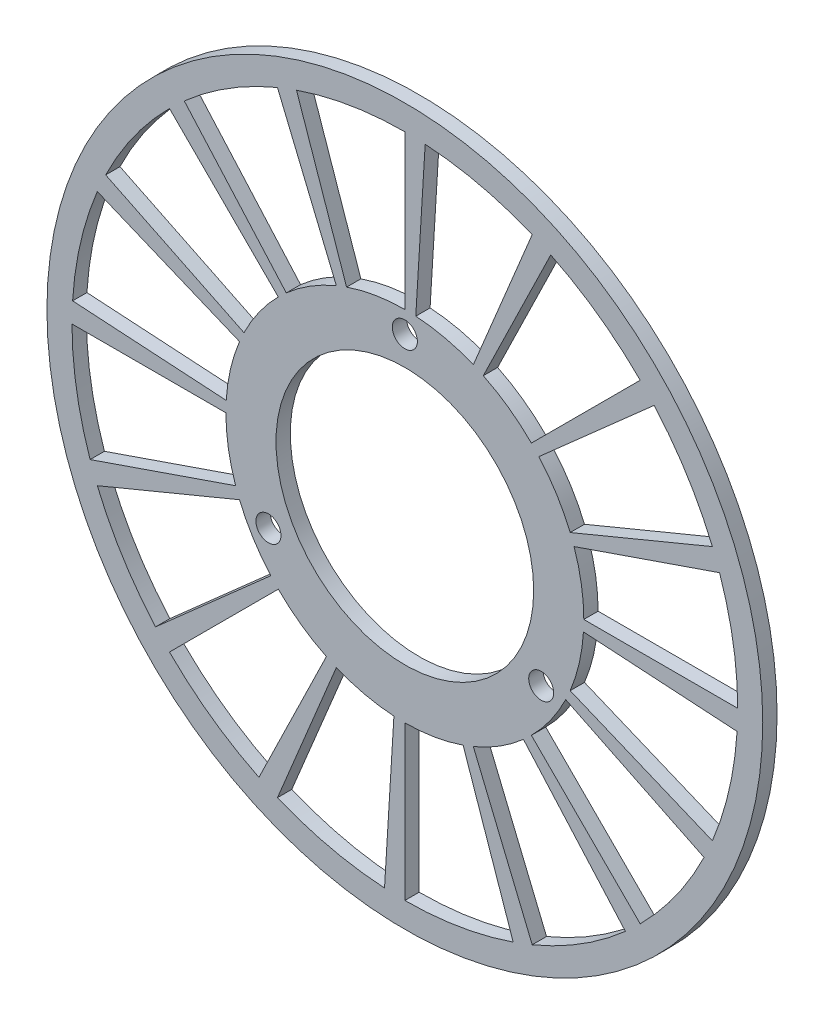
SolidWorks part; units mm, degrees
ref_plane "Front Plane" through (0, 0, 0) normal (0, 0, 1) x (1, 0, 0)
ref_plane "Top Plane" through (0, 0, 0) normal (0, 1, 0) x (1, 0, 0)
ref_plane "Right Plane" through (0, 0, 0) normal (1, 0, 0) x (0, 0, -1)
sketch "Sketch1" plane through (0, 0, 0) normal (0, 0, 1) x (1, 0, 0)
  line L0 (0, 0) -> (46.5, 0) construction
  line L1 (0, 0) -> (43.9666, 15.1389) construction
  line L2 (25, 0) -> (46.5, 0)
  line L3 (23.638, 8.1392) -> (43.9666, 15.1389)
  line L4 (0, 0) -> (46, 0) construction
  line L5 (0, 0) -> (43.7486, 14.2148) construction
  line L6 (25, 0) -> (46, 0) construction
  line L7 (23.7764, 7.7254) -> (43.7486, 14.2148) construction
  line L8 (23.097, -9.5671) -> (42.9604, -17.7948)
  line L9 (24.9534, -1.5262) -> (46.4133, -2.8388)
  line L10 (17.6777, -17.6777) -> (32.8805, -32.8805)
  line L11 (22.4699, -10.9593) -> (41.7939, -20.3843)
  line L12 (9.5671, -23.097) -> (17.7948, -42.9604)
  line L13 (16.5655, -18.7239) -> (30.8118, -34.8264)
  line L14 (0, -25) -> (0, -46.5)
  line L15 (8.1392, -23.638) -> (15.1389, -43.9666)
  line L16 (-9.5671, -23.097) -> (-17.7948, -42.9604)
  line L17 (-1.5262, -24.9534) -> (-2.8388, -46.4133)
  line L18 (-17.6777, -17.6777) -> (-32.8805, -32.8805)
  line L19 (-10.9593, -22.4699) -> (-20.3843, -41.7939)
  line L20 (-23.097, -9.5671) -> (-42.9604, -17.7948)
  line L21 (-18.7239, -16.5655) -> (-34.8264, -30.8118)
  line L22 (-25, 0) -> (-46.5, 0)
  line L23 (-23.638, -8.1392) -> (-43.9666, -15.1389)
  line L24 (-23.097, 9.5671) -> (-42.9604, 17.7948)
  line L25 (-24.9534, 1.5262) -> (-46.4133, 2.8388)
  line L26 (-17.6777, 17.6777) -> (-32.8805, 32.8805)
  line L27 (-22.4699, 10.9593) -> (-41.7939, 20.3843)
  line L28 (-9.5671, 23.097) -> (-17.7948, 42.9604)
  line L29 (-16.5655, 18.7239) -> (-30.8118, 34.8264)
  line L30 (0, 25) -> (0, 46.5)
  line L31 (-8.1392, 23.638) -> (-15.1389, 43.9666)
  line L32 (9.5671, 23.097) -> (17.7948, 42.9604)
  line L33 (1.5262, 24.9534) -> (2.8388, 46.4133)
  line L34 (17.6777, 17.6777) -> (32.8805, 32.8805)
  line L35 (10.9593, 22.4699) -> (20.3843, 41.7939)
  line L36 (23.097, 9.5671) -> (42.9604, 17.7948)
  line L37 (18.7239, 16.5655) -> (34.8264, 30.8118)
  circle A0 centre (0, 0) radius 50
  circle A1 centre (0, 0) radius 18
  circle A2 centre (0, 0) radius 25 construction
  circle A3 centre (0, 0) radius 46.5 construction
  arc A4 (25, 0) -> (23.638, 8.1392) centre (0, 0) ccw
  arc A5 (46.5, 0) -> (43.9666, 15.1389) centre (0, 0) ccw
  circle A6 centre (0, 0) radius 22 construction
  circle A7 centre (0, 0) radius 22 construction
  circle A8 centre (0, 22) radius 1.75
  circle A13 centre (19.0526, -11) radius 1.75
  circle A14 centre (-19.0526, -11) radius 1.75
  circle A15 centre (0, 0) radius 25 construction
  circle A16 centre (0, 0) radius 46 construction
  arc A17 (25, 0) -> (23.7764, 7.7254) centre (0, 0) ccw construction
  arc A18 (46, 0) -> (43.7486, 14.2148) centre (0, 0) ccw construction
  arc A19 (23.097, -9.5671) -> (24.9534, -1.5262) centre (0, 0) ccw
  arc A20 (42.9604, -17.7948) -> (46.4133, -2.8388) centre (0, 0) ccw
  arc A21 (17.6777, -17.6777) -> (22.4699, -10.9593) centre (0, 0) ccw
  arc A22 (32.8805, -32.8805) -> (41.7939, -20.3843) centre (0, 0) ccw
  arc A23 (9.5671, -23.097) -> (16.5655, -18.7239) centre (0, 0) ccw
  arc A24 (17.7948, -42.9604) -> (30.8118, -34.8264) centre (0, 0) ccw
  arc A25 (0, -25) -> (8.1392, -23.638) centre (0, 0) ccw
  arc A26 (0, -46.5) -> (15.1389, -43.9666) centre (0, 0) ccw
  arc A27 (-9.5671, -23.097) -> (-1.5262, -24.9534) centre (0, 0) ccw
  arc A28 (-17.7948, -42.9604) -> (-2.8388, -46.4133) centre (0, 0) ccw
  arc A29 (-17.6777, -17.6777) -> (-10.9593, -22.4699) centre (0, 0) ccw
  arc A30 (-32.8805, -32.8805) -> (-20.3843, -41.7939) centre (0, 0) ccw
  arc A31 (-23.097, -9.5671) -> (-18.7239, -16.5655) centre (0, 0) ccw
  arc A32 (-42.9604, -17.7948) -> (-34.8264, -30.8118) centre (0, 0) ccw
  arc A33 (-25, 0) -> (-23.638, -8.1392) centre (0, 0) ccw
  arc A34 (-46.5, 0) -> (-43.9666, -15.1389) centre (0, 0) ccw
  arc A35 (-23.097, 9.5671) -> (-24.9534, 1.5262) centre (0, 0) ccw
  arc A36 (-42.9604, 17.7948) -> (-46.4133, 2.8388) centre (0, 0) ccw
  arc A37 (-17.6777, 17.6777) -> (-22.4699, 10.9593) centre (0, 0) ccw
  arc A38 (-32.8805, 32.8805) -> (-41.7939, 20.3843) centre (0, 0) ccw
  arc A39 (-9.5671, 23.097) -> (-16.5655, 18.7239) centre (0, 0) ccw
  arc A40 (-17.7948, 42.9604) -> (-30.8118, 34.8264) centre (0, 0) ccw
  arc A41 (0, 25) -> (-8.1392, 23.638) centre (0, 0) ccw
  arc A42 (0, 46.5) -> (-15.1389, 43.9666) centre (0, 0) ccw
  arc A43 (9.5671, 23.097) -> (1.5262, 24.9534) centre (0, 0) ccw
  arc A44 (17.7948, 42.9604) -> (2.8388, 46.4133) centre (0, 0) ccw
  arc A45 (17.6777, 17.6777) -> (10.9593, 22.4699) centre (0, 0) ccw
  arc A46 (32.8805, 32.8805) -> (20.3843, 41.7939) centre (0, 0) ccw
  arc A47 (23.097, 9.5671) -> (18.7239, 16.5655) centre (0, 0) ccw
  arc A48 (42.9604, 17.7948) -> (34.8264, 30.8118) centre (0, 0) ccw
  point P20 (0, 0)
  point P22 (0, 2.774)
  point P23 (0, 0)
  point P90 (0, 0)
  dimension "D1" = 50
  dimension "D2" = 93
  dimension "D4" = 44
  dimension "D5" = 36
  dimension "D6" = 3.5
  dimension "D8" = 100
  dimension "D9" = 16
  dimension "D10" = 92
  dimension "D3" = 19
  dimension "D11" = 18
  dimension "D7" = 3
extrude "Boss-Extrude1" add sketch "Sketch1" along normal blind 2
